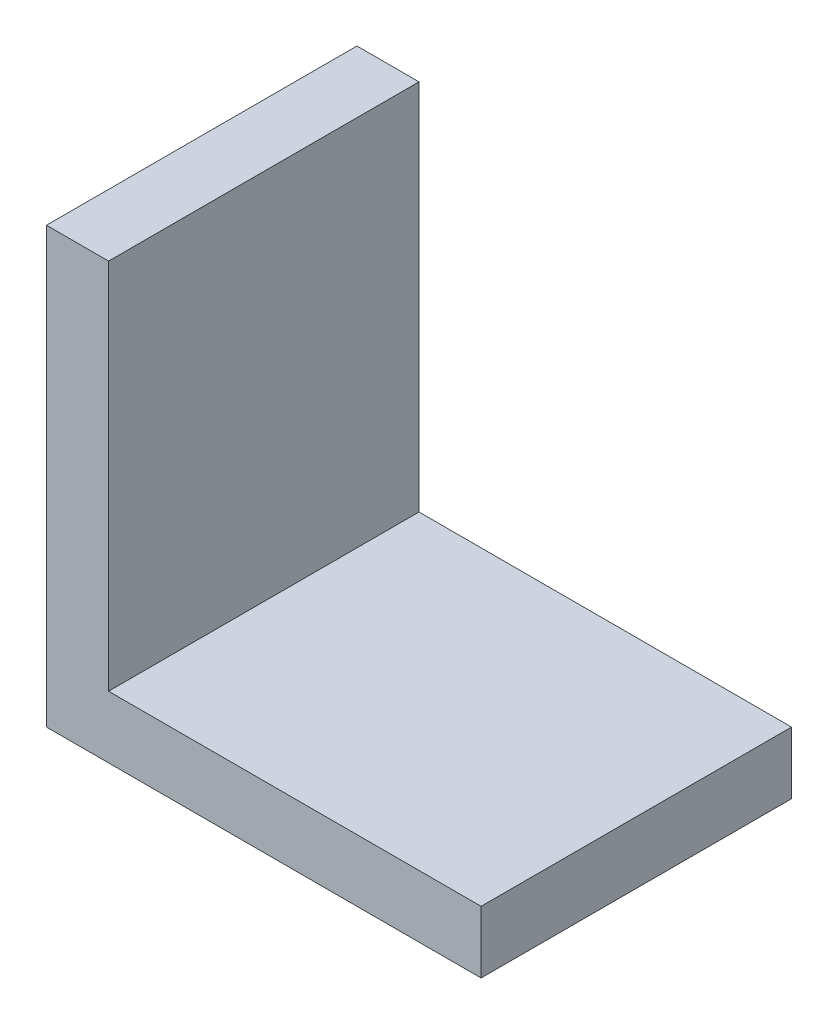
SolidWorks part; units mm, degrees
ref_plane "Front Plane" through (0, 0, 0) normal (0, 0, 1) x (1, 0, 0)
ref_plane "Top Plane" through (0, 0, 0) normal (0, 1, 0) x (1, 0, 0)
ref_plane "Right Plane" through (0, 0, 0) normal (1, 0, 0) x (0, 0, -1)
sketch "Sketch1" plane through (0, 0, 0) normal (0, 0, 1) x (1, 0, 0)
  line L0 (0, 0) -> (0, 28)
  line L1 (0, 28) -> (4, 28)
  line L2 (4, 28) -> (4, 4)
  line L3 (4, 4) -> (28, 4)
  line L4 (28, 4) -> (28, 0)
  line L5 (28, 0) -> (0, 0)
  dimension "D1" = 28
  dimension "D2" = 28
  dimension "D3" = 4
  dimension "D4" = 4
extrude "Boss-Extrude1" add sketch "Sketch1" along normal blind 20
sketch "Sketch5" plane through (0, 0, 0) normal (-1, 0, 0) x (0, 0, 1)
  line L0 (20, 28) -> (20, 0) construction
  line L1 (0, 0) -> (20, 0)
  line L2 (0, 0) -> (0, 28)
  line L3 (0, 28) -> (20, 28)
  line L4 (20, 0) -> (20, 28)
  circle A0 centre (10, 14) radius 2.5
  point P9 (0, 0)
  dimension "D1" = 5
extrude "Boss-Extrude6" add sketch "Sketch5" along normal blind 6.4 contours A0
sketch "Sketch6" plane through (0, 0, 0) normal (0, -1, 0) x (1, 0, 0)
  line L1 (0, 0) -> (28, 0)
  line L2 (0, 0) -> (0, 20)
  line L3 (0, 20) -> (28, 20)
  line L4 (28, 0) -> (28, 20)
  circle A0 centre (14, 10) radius 2.5
  dimension "D1" = 5
extrude "Boss-Extrude7" add sketch "Sketch6" along normal blind 6.4 contours A0
